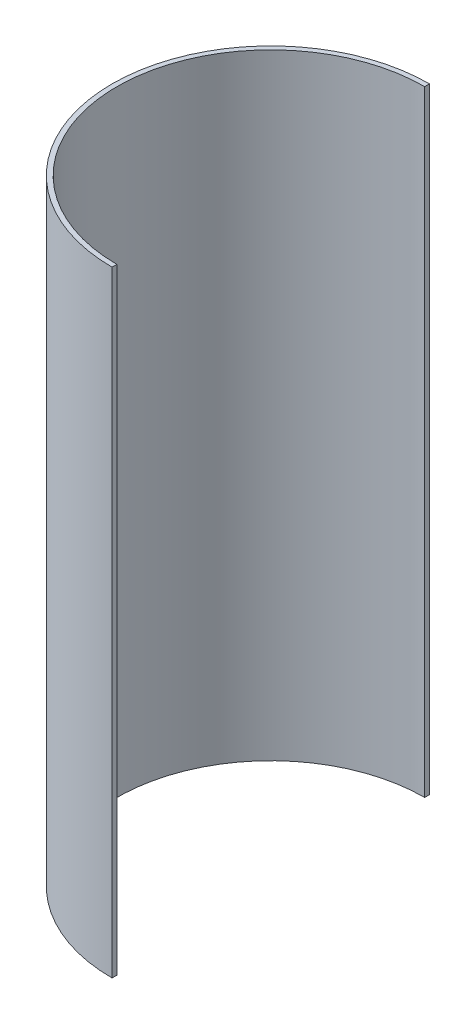
SolidWorks part; units mm, degrees
ref_plane "Front Plane" through (0, 0, 0) normal (0, 0, 1) x (1, 0, 0)
ref_plane "Top Plane" through (0, 0, 0) normal (0, 1, 0) x (1, 0, 0)
ref_plane "Right Plane" through (0, 0, 0) normal (1, 0, 0) x (0, 0, -1)
sketch "Sketch1" plane through (0, 0, 0) normal (0, 1, 0) x (1, 0, 0)
  line L3 (0, 101.6) -> (0, 104.775)
  line L5 (0, -104.775) -> (0, -101.6)
  arc A1 (0, 101.6) -> (0, -101.6) centre (0, 0) ccw
  arc A3 (0, 104.775) -> (0, -104.775) centre (0, 0) ccw
  dimension "D1" = 101.6
  dimension "D2" = 104.775
extrude "Boss-Extrude1" add sketch "Sketch1" along normal blind 406.4
